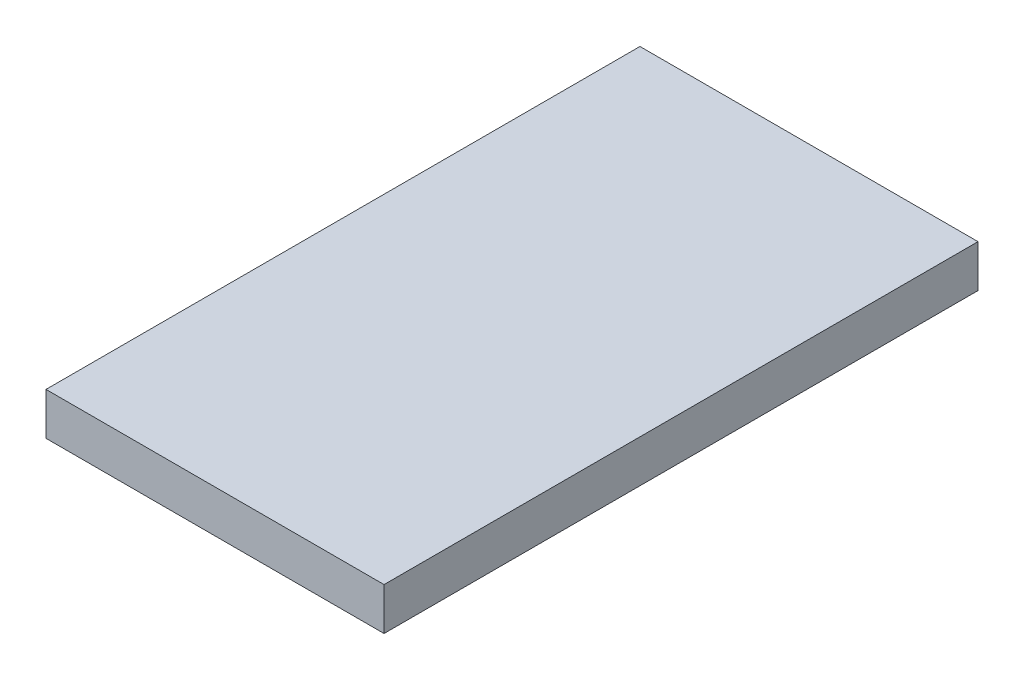
SolidWorks part; units mm, degrees
ref_plane "Front Plane" through (0, 0, 0) normal (0, 0, 1) x (1, 0, 0)
ref_plane "Top Plane" through (0, 0, 0) normal (0, 1, 0) x (1, 0, 0)
ref_plane "Right Plane" through (0, 0, 0) normal (1, 0, 0) x (0, 0, -1)
sketch "Sketch1" plane through (0, 0, 0) normal (0, 1, 0) x (1, 0, 0)
  line L0 (363.0116, 530.3309) -> (1607.4617, 530.3309) construction
  line L10 (0, 0) -> (167.4187, 0)
  line L11 (0, 0) -> (0, 294.1531)
  line L12 (0, 294.1531) -> (167.4187, 294.1531)
  line L13 (167.4187, 0) -> (167.4187, 294.1531)
  point P2 (0, 0)
  point P3 (0, 0)
  point P4 (173.8935, 289.8366)
  point P16 (0, 0)
extrude "Boss-Extrude1" add sketch "Sketch1" along normal blind 21
